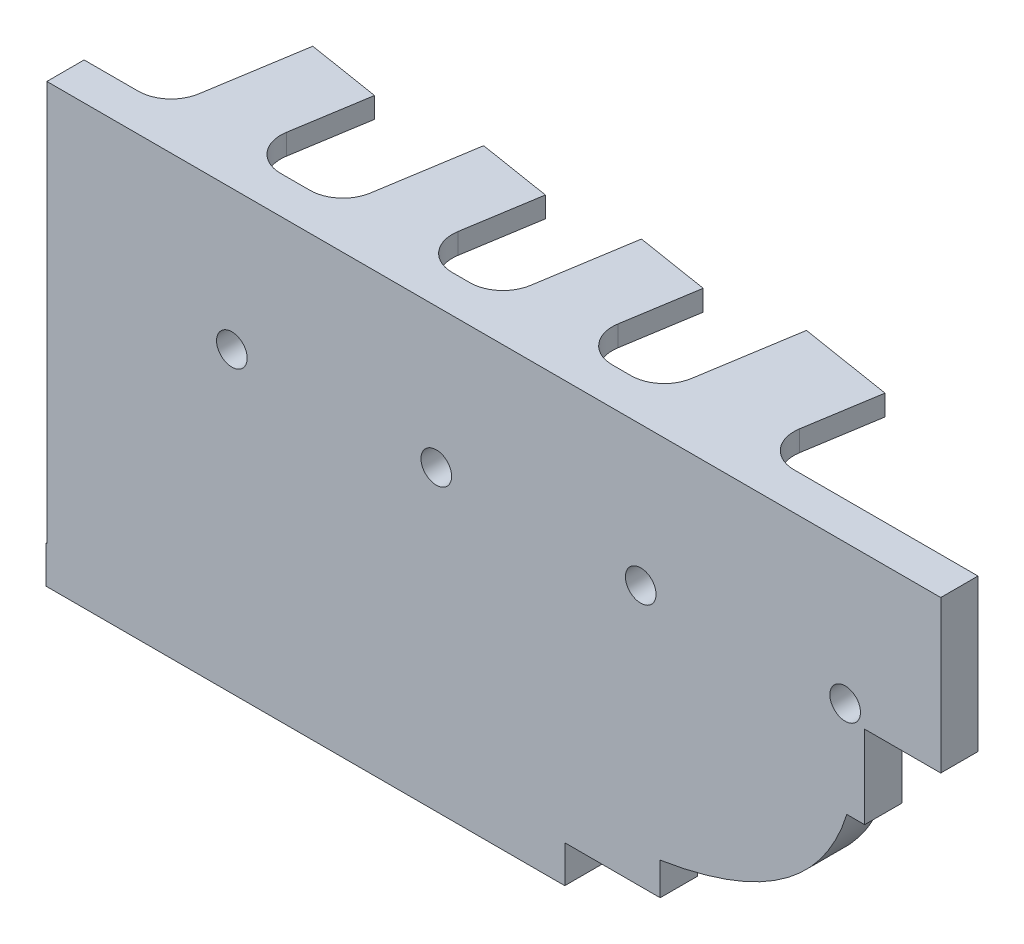
SolidWorks part; units mm, degrees
ref_plane "Front Plane" through (0, 0, 0) normal (0, 0, 1) x (1, 0, 0)
ref_plane "Top Plane" through (0, 0, 0) normal (0, 1, 0) x (1, 0, 0)
ref_plane "Right Plane" through (0, 0, 0) normal (1, 0, 0) x (0, 0, -1)
sketch "Sketch1" plane through (0, 0, 0) normal (0, 0, 1) x (1, 0, 0)
  line L0 (24.7, 21) -> (0, 21)
  line L1 (24.7, 21) -> (24.7, 0)
  line L2 (24.7, 0) -> (0, 0)
  line L3 (0, 21) -> (0, 0)
  circle A0 centre (22.85, 18.5) radius 1.05
  circle A1 centre (22.85, 15.5) radius 1.05
  circle A2 centre (22.35, 11.5) radius 1.85
  circle A3 centre (20.35, 8.5) radius 1.05
  circle A4 centre (20.35, 6.1667) radius 1.05
  circle A5 centre (20.35, 3.8333) radius 1.05
  circle A6 centre (20.35, 1.5) radius 1.05
  circle A7 centre (4.35, 8.5) radius 1.05
  circle A8 centre (4.35, 6.1667) radius 1.05
  circle A9 centre (4.35, 3.8333) radius 1.05
  circle A10 centre (4.35, 1.5) radius 1.05
  dimension "D3" = 2.1
  dimension "D4" = 2.1
  dimension "D5" = 2.1
  dimension "D6" = 2.1
  dimension "D7" = 2.1
  dimension "D8" = 2.1
  dimension "D9" = 2.1
  dimension "D10" = 2.1
  dimension "D11" = 3.7
  dimension "D12" = 2.1
  dimension "D13" = 2.1
  dimension "D1" = 24.7
  dimension "D2" = 21
  dimension "D15" = 4.35
  dimension "D16" = 2.3333
  dimension "D19" = 1.5
  dimension "D20" = 4.35
  dimension "D21" = 2.3333
  dimension "D22" = 2.3333
  dimension "D23" = 2.3333
  dimension "D24" = 3.6056
  dimension "D25" = 2.5
  dimension "D26" = 1.85
  dimension "D27" = 3
  dimension "D28" = 22.35
extrude "Boss-Extrude1" add sketch "Sketch1" along normal blind 2
pattern_linear "LPattern1" count 4 spacing 24.7 along (-1, 0, 0) of "Boss-Extrude1"
sketch "Sketch3" plane through (0, 0, 2) normal (0, 0, 1) x (1, 0, 0)
  line L1 (-74.1, 21) -> (24.7, 21)
  line L2 (-74.1, 21) -> (-74.1, 0)
  line L3 (-74.1, 0) -> (24.7, 0)
  line L4 (24.7, 21) -> (24.7, 0)
  circle A0 centre (-51.75, 11.5) radius 1.85
  circle A1 centre (-27.05, 11.5) radius 1.85
  circle A2 centre (-2.35, 11.5) radius 1.85
  circle A3 centre (22.35, 11.5) radius 1.85
  dimension "D1" = 3.7
  dimension "D2" = 3.7
  dimension "D3" = 3.7
  dimension "D4" = 3.7
extrude "Boss-Extrude2" add sketch "Sketch3" along normal blind 2.5 contours L2 L1 L4 L3 | A0 | A1 | A2 | A3
sketch "Sketch4" plane through (0, 21, 0) normal (0, 1, 0) x (1, 0, 0)
  line L1 (-74.1, 0) -> (24.7, 0)
  line L2 (-74.1, 0) -> (-74.1, -4.5)
  line L3 (-74.1, -4.5) -> (24.7, -4.5)
  line L4 (24.7, 0) -> (24.7, -4.5)
extrude "Boss-Extrude3" add sketch "Sketch4" along normal blind 7.3677
sketch "Sketch6" plane through (24.7, 0, 0) normal (1, 0, 0) x (0, 0, -1)
  line L0 (-4.5, 10) -> (0, 10)
  line L1 (-4.5, 28.3677) -> (0, 28.3677)
  line L2 (-4.5, 28.3677) -> (-4.5, 0)
  line L3 (-4.5, 0) -> (0, 0)
  line L4 (0, 28.3677) -> (0, 0)
  line M5 (0, 0) -> (0, 28.3677)
  line M6 (0, 28.3677) -> (-4.5, 28.3677)
  line M7 (-4.5, 28.3677) -> (-4.5, 0)
  dimension "D1" = 10
extrude "Boss-Extrude4" add sketch "Sketch6" along normal blind 9.198 contours L0 M7 M5 M6
sketch "Sketch7" plane through (0, 0, 0) normal (0, -1, 0) x (1, 0, 0)
  line L1 (-74.1, 4.5) -> (0, 4.5)
  line L2 (-74.1, 4.5) -> (-74.1, 0)
  line L3 (-74.1, 0) -> (0, 0)
  line L4 (0, 4.5) -> (0, 0)
extrude "Boss-Extrude5" add sketch "Sketch7" along normal blind 20
sketch "Sketch8" plane through (0, -20, 0) normal (0, -1, 0) x (1, 0, 0)
  line L0 (0, 4.5) -> (-74.1, 4.5) construction
  line L1 (-64.7064, 4.5) -> (-11.5279, 4.5)
  line L2 (-64.7064, 4.5) -> (-64.7064, 0)
  line L3 (-64.7064, 0) -> (-11.5279, 0)
  line L4 (-11.5279, 4.5) -> (-11.5279, 0)
  line L5 (-74.1, 0) -> (0, 0) construction
extrude "Boss-Extrude6" add sketch "Sketch8" along normal blind 4.5
sketch "Sketch9" plane through (0, 0, 4.5) normal (0, 0, 1) x (1, 0, 0)
  line L0 (0, -20) -> (0, 0) construction
  line L1 (0, 0) -> (24.7, 0) construction
  line L2 (0, -16.0595) -> (0, 0)
  line L3 (0, 0) -> (22.5482, 0)
  spline S0 degree 2 poles (0, -16.0595) (19.3219, -12.9635) (22.8867, 1.2075) knots 0 0 0 1 1 1
  line M7 (0, -20) -> (0, 0)
  line M8 (0, 0) -> (24.7, 0)
extrude "Boss-Extrude7" add sketch "Sketch9" against normal blind 4.75 contours S0 M7 M8
sketch "Sketch10" plane through (0, 28.3677, 0) normal (0, 1, 0) x (1, 0, 0)
  line L0 (-74.1, -4.5) -> (33.898, -4.5) construction
  line L1 (-64.8873, -4.5) -> (-74.1, -4.5)
  line L2 (-64.8873, -4.5) -> (-61.722, 15.2479)
  line L3 (-61.722, 15.2479) -> (-52.8354, 13.8236)
  line L5 (-52.8354, 13.8236) -> (-55.0511, 0)
  line L6 (-55.0511, 0) -> (-43.4213, 0)
  line L7 (-43.4213, 0) -> (-40.991, 15.1619)
  line L8 (-40.991, 15.1619) -> (-32.1045, 13.7375)
  line L9 (-32.1045, 13.7375) -> (-34.3064, 0)
  line L10 (-34.3064, 0) -> (-24.0864, 0)
  line L11 (-24.0864, 0) -> (-21.6935, 14.9291)
  line L12 (-21.6935, 14.9291) -> (-12.807, 13.5047)
  line L13 (-12.807, 13.5047) -> (-15.0365, -0.4051)
  line L14 (-15.0365, -0.4051) -> (-4.6192, 0)
  line L15 (-4.6192, 0) -> (-2.1613, 15.3345)
  line L16 (-2.1613, 15.3345) -> (9.1423, 13.5227)
  line L17 (9.1423, 13.5227) -> (6.9748, 0)
  line L18 (6.9748, 0) -> (6.9748, -4.5)
  line L19 (6.9748, -4.5) -> (-64.8873, -4.5)
  line M3 (-74.1, -4.5) -> (33.898, -4.5)
  dimension "D2" = 71.8621
  dimension "D3" = 4.5
  dimension "D4" = 13.6954
  dimension "D5" = 11.4479
  dimension "D6" = 15.5303
  dimension "D7" = 10.4251
  dimension "D8" = 14.0873
  dimension "D9" = 9
  dimension "D10" = 15.1196
  dimension "D11" = 10.22
  dimension "D12" = 13.9129
  dimension "D13" = 9
  dimension "D14" = 15.3554
  dimension "D15" = 11.6299
  dimension "D16" = 14
  dimension "D17" = 9
  dimension "D18" = 20
  dimension "D19" = 9.2127
extrude "Boss-Extrude8" add sketch "Sketch10" against normal blind 2.5 contours L17 L16 L15 M3 | L13 L12 L11 M3 | L9 L8 L7 M3 | L5 L3 L2 M3
sketch "Sketch14" plane through (-64.7064, 0, 0) normal (-1, 0, 0) x (0, 0, 1)
  line L1 (4.5, -24.5) -> (0, -24.5)
  line L2 (4.5, -24.5) -> (4.5, -20)
  line L3 (4.5, -20) -> (0, -20)
  line L4 (0, -24.5) -> (0, -20)
extrude "Boss-Extrude9" add sketch "Sketch14" along normal blind 9.5
fillet "Fillet1" radius 4 8 edges at (6.9748, 27.1177, 0) (-4.6192, 27.1177, 0) (-14.9716, 27.1177, 0) (-24.0864, 27.1177, 0) (-34.3064, 27.1177, 0) (-43.4213, 27.1177, 0) (-55.0511, 27.1177, 0) (-64.166, 27.1177, 0)
